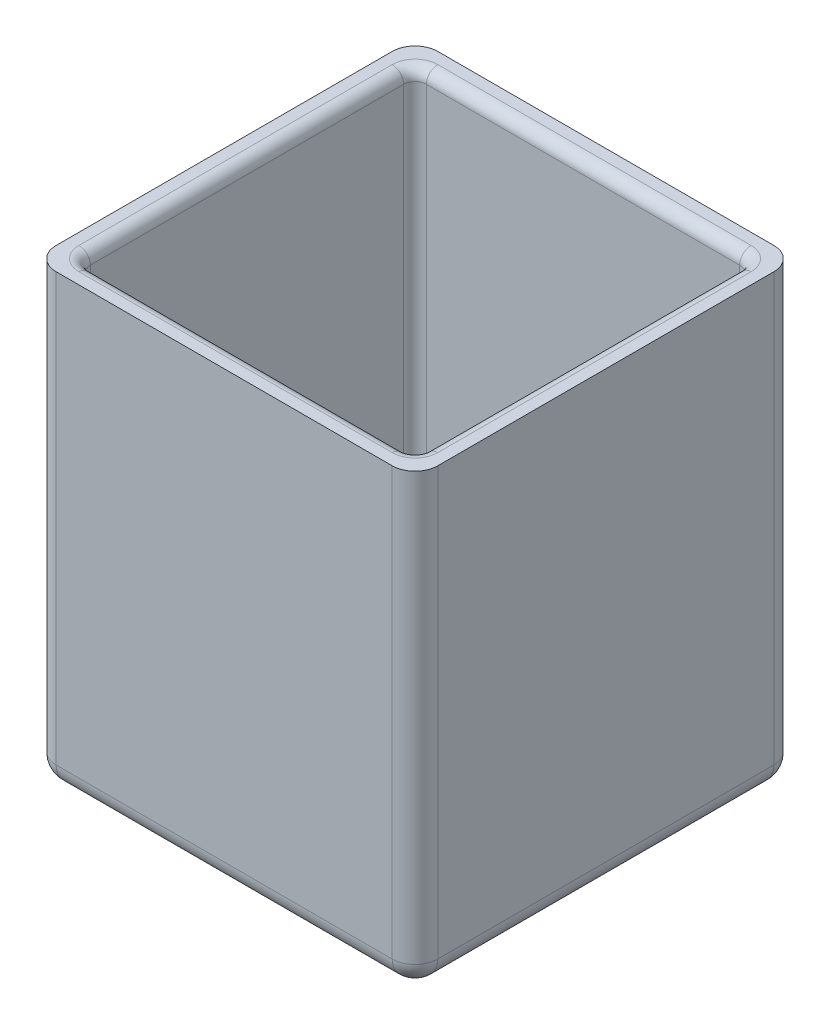
SolidWorks part; units mm, degrees
material "PBT General Purpose"
ref_plane "Front Plane" through (0, 0, 0) normal (0, 0, 1) x (1, 0, 0)
ref_plane "Top Plane" through (0, 0, 0) normal (0, 1, 0) x (1, 0, 0)
ref_plane "Right Plane" through (0, 0, 0) normal (1, 0, 0) x (0, 0, -1)
sketch "Sketch1" plane through (0, 0, 0) normal (0, 1, 0) x (1, 0, 0)
  line L0 (0, 0) -> (33.5, 0)
  line L1 (0, 0) -> (0, 33.5)
  line L2 (33.5, 0) -> (33.5, 33.5)
  line L3 (0, 33.5) -> (33.5, 33.5)
  line L4 (2, 31.5) -> (31.5, 31.5)
  line L5 (2, 31.5) -> (2, 2)
  line L6 (31.5, 31.5) -> (31.5, 2)
  line L7 (2, 2) -> (31.5, 2)
  dimension "D1" = 2
  dimension "D2" = 2
  dimension "D3" = 2
  dimension "D4" = 2
  dimension "D5" = 29.5
  dimension "D6" = 29.5
extrude "Boss-Extrude1" add sketch "Sketch1" along normal blind 39.5
sketch "Sketch2" plane through (0, 0, 0) normal (0, -1, 0) x (1, 0, 0)
  line L0 (31.5, -31.5) -> (31.5, -2) construction
  line L1 (2, -2) -> (31.5, -2) construction
  line L2 (2, -31.5) -> (2, -2) construction
  line L3 (2, -31.5) -> (31.5, -31.5) construction
  line L4 (31.5, -31.5) -> (31.5, -2)
  line L5 (2, -2) -> (31.5, -2)
  line L6 (2, -31.5) -> (2, -2)
  line L7 (2, -31.5) -> (31.5, -31.5)
extrude "Boss-Extrude2" add sketch "Sketch2" against normal blind 3
fillet "Скругление1" radius 2 4 edges at (0, 19.75, -33.5) (0, 19.75, 0) (33.5, 19.75, -33.5) (33.5, 19.75, 0)
fillet "Скругление2" radius 2 8 edges at (32.9142, 0, -0.5858) (16.75, 0, 0) (0.5858, 0, -0.5858) (0, 0, -16.75) (0.5858, 0, -32.9142) (16.75, 0, -33.5) (32.9142, 0, -32.9142) (33.5, 0, -16.75)
sketch "Эскиз1" plane through (0, 0, 0) normal (0, -1, 0) x (1, 0, 0)
  line L0 (2, -16.75) -> (31.5, -16.75) construction
  line L1 (2, -2) -> (2, -31.5) construction
  line L2 (31.5, -31.5) -> (31.5, -2) construction
  line L3 (16.75, -2) -> (16.75, -31.5) construction
  line L4 (31.5, -2) -> (2, -2) construction
  line L5 (2, -31.5) -> (31.5, -31.5) construction
fillet "Скругление3" radius 1 12 edges at (16.75, 39.5, -2) (31.5, 39.5, -16.75) (2, 39.5, -16.75) (31.5, 3, -16.75) (16.75, 3, -2) (2, 3, -16.75) (16.75, 39.5, -31.5) (31.5, 21.25, -31.5) (16.75, 3, -31.5) (2, 21.25, -31.5) (31.5, 21.25, -2) (2, 21.25, -2)
